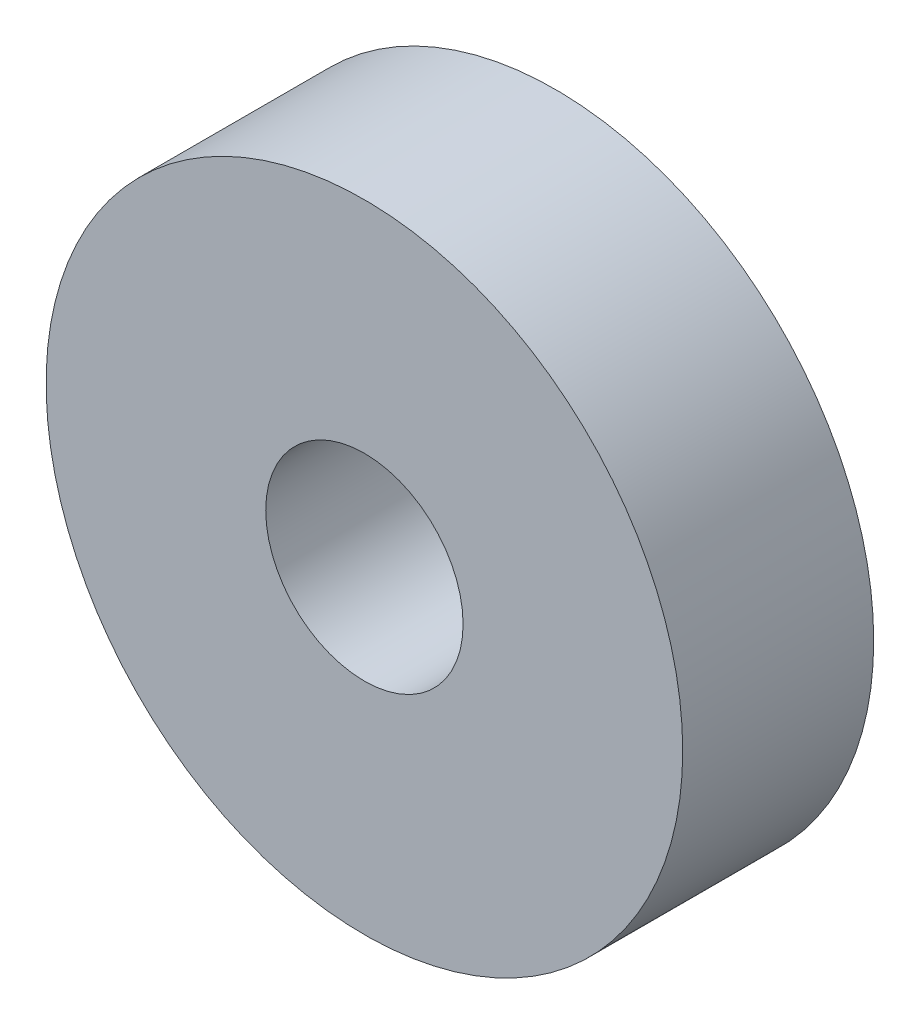
SolidWorks part; units mm, degrees
ref_plane "Front Plane" through (0, 0, 0) normal (0, 0, 1) x (1, 0, 0)
ref_plane "Top Plane" through (0, 0, 0) normal (0, 1, 0) x (1, 0, 0)
ref_plane "Right Plane" through (0, 0, 0) normal (1, 0, 0) x (0, 0, -1)
sketch "Model" plane through (0, 0, 0) normal (0, 0, 1) x (1, 0, 0)
  circle A0 centre (42, 46) radius 1.55
  circle A1 centre (42, 46) radius 5
extrude "Boss-Extrude1" add sketch "Model" along normal blind 3
